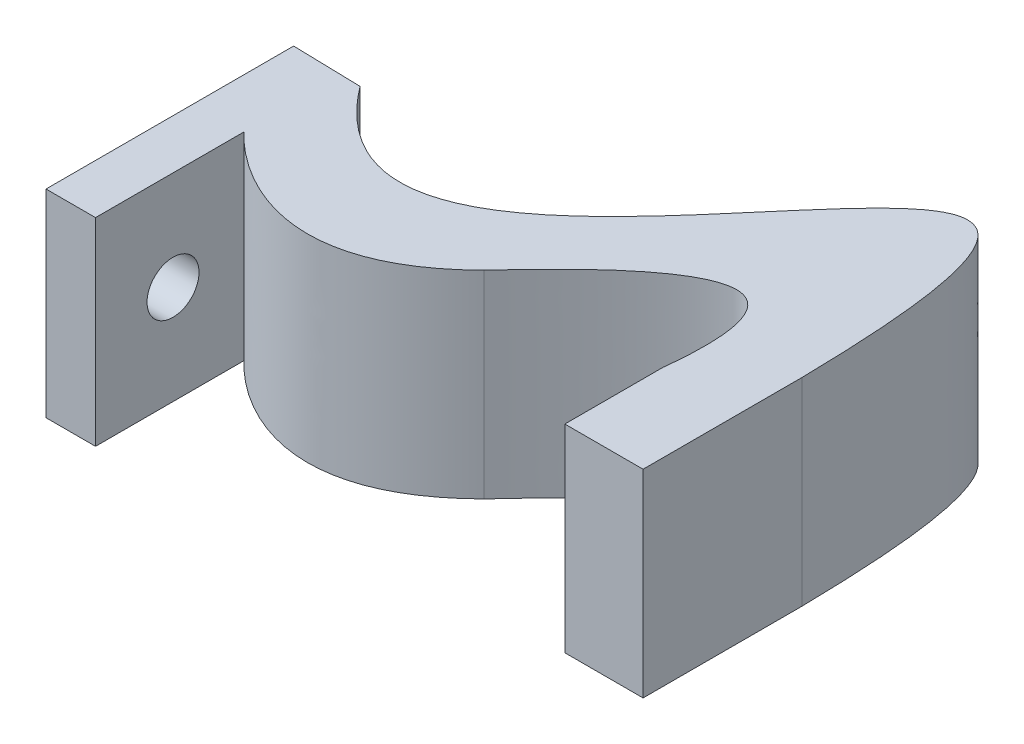
SolidWorks part; units mm, degrees
ref_plane "Front Plane" through (0, 0, 0) normal (0, 0, 1) x (1, 0, 0)
ref_plane "Top Plane" through (0, 0, 0) normal (0, 1, 0) x (1, 0, 0)
ref_plane "Right Plane" through (0, 0, 0) normal (1, 0, 0) x (0, 0, -1)
sketch "Sketch1" plane through (0, 0, 0) normal (0, 1, 0) x (1, 0, 0)
  line L0 (-24.1994, 0) -> (-24.1994, -4.8248)
  line L1 (23.6337, 0) -> (-24.1994, 0) construction
  line L2 (17.5363, -9.3626) -> (25.4363, -9.3626)
  line L3 (-29.1994, -4.8248) -> (-29.1994, 9.9958)
  line L4 (-29.1994, 9.9958) -> (-22.3224, 9.8223)
  line L5 (25.4363, -9.3626) -> (25.4363, 28.1393) construction
  line L6 (25.4363, 6.6595) -> (25.4363, -9.3626)
  line L7 (17.5363, -9.3626) -> (17.5363, 0.5463)
  line L8 (-29.1994, -4.8248) -> (-29.1994, -15.0042)
  line L9 (-29.1994, -15.0042) -> (-24.1994, -15.0042)
  line L10 (-24.1994, -15.0042) -> (-24.1994, -4.8248)
  spline S0 degree 3 poles (-24.1994, 0) (-24.1978, -0.0019) (-13.034, -12.8901) (0, 0) knots 0 0 0 0 1 1 1 1
  spline S1 degree 2 poles (0, 0) (19.899, 21.8419) (17.5363, 0.5463) knots 0 0 0 1 1 1
  spline S2 degree 3 poles (-22.3224, 9.8223) (0.2326, -19.9409) (24.4676, 67.6816) (25.4363, 6.6595) knots 0 0 0 0 1 1 1 1
  dimension "D1" = 27.5
  dimension "D2" = 25
  dimension "D5" = 10
  dimension "D7" = 5
extrude "Boss-Extrude3" add sketch "Sketch1" along normal blind 20
sketch "Sketch3" plane through (-24.1994, 0, 0) normal (1, 0, 0) x (0, 0, -1)
  line L0 (-15.0042, 10) -> (-7.1819, 10) construction
  line L1 (-15.0042, 20) -> (-15.0042, 0) construction
  circle A0 centre (-7.1819, 10) radius 2.625
  dimension "D1" = 5.25
extrude "Cut-Extrude1" cut sketch "Sketch3" against normal through all
sketch "Sketch4" plane through (-29.1994, 0, 0) normal (-1, 0, 0) x (0, 0, 1)
  line L0 (-9.9958, 10) -> (15.0042, 10) construction
  line L1 (-9.9958, 20) -> (-9.9958, 0) construction
  line L2 (15.0042, 20) -> (15.0042, 0) construction
  line L4 (-6.4985, 12.5) -> (2.3248, 12.5)
  line L5 (-6.4985, 12.5) -> (-6.4985, 7.5)
  line L6 (-6.4985, 7.5) -> (2.3248, 7.5)
  line L7 (2.3248, 12.5) -> (2.3248, 7.5)
  line L8 (-6.4985, 12.5) -> (2.3248, 7.5) construction
  line L9 (-6.4985, 7.5) -> (2.3248, 12.5) construction
  point P6 (-2.0869, 10)
  dimension "D1" = 5
extrude "Boss-Extrude4" add sketch "Sketch4" along normal blind 0.5
